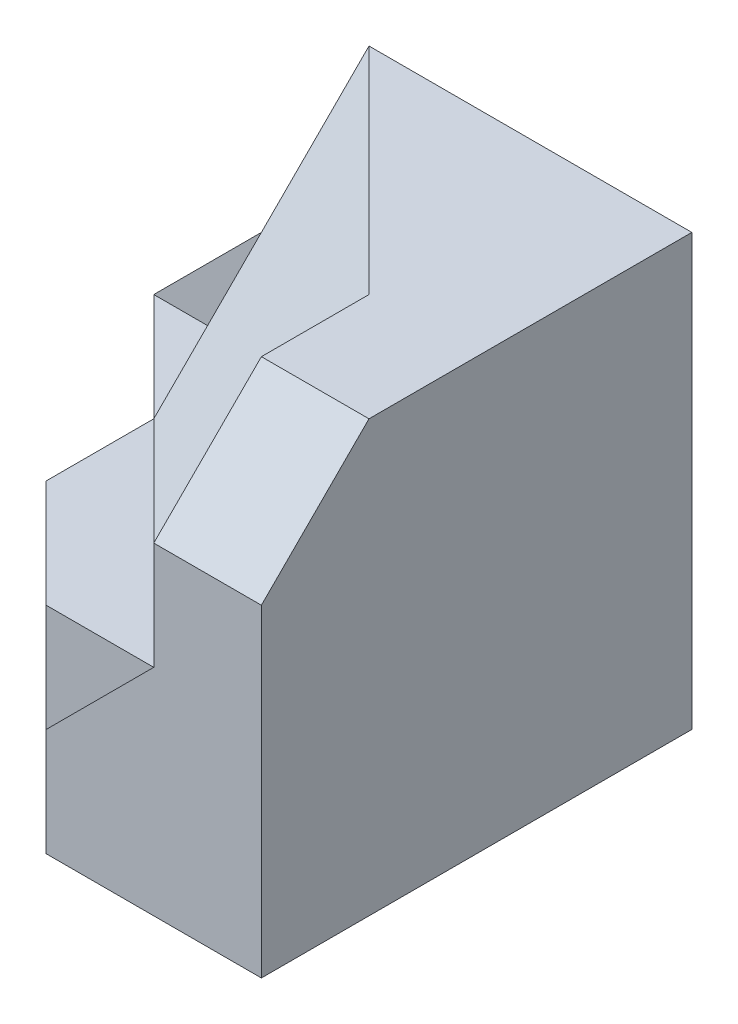
SolidWorks part; units mm, degrees
ref_plane "Front Plane" through (0, 0, 0) normal (0, 0, 1) x (1, 0, 0)
ref_plane "Top Plane" through (0, 0, 0) normal (0, 1, 0) x (1, 0, 0)
ref_plane "Right Plane" through (0, 0, 0) normal (1, 0, 0) x (0, 0, -1)
sketch "Sketch1" plane through (0, 0, 0) normal (0, 1, 0) x (1, 0, 0)
  line L0 (-15, 0) -> (0, 0)
  line L1 (0, 0) -> (0, -15)
  line L2 (0, -15) -> (-5, -15)
  line L3 (-5, -15) -> (-5, -10)
  line L4 (-5, -10) -> (-15, 0)
  dimension "D1" = 5
  dimension "D2" = 5
  dimension "D3" = 15
  dimension "D4" = 15
extrude "Boss-Extrude1" add sketch "Sketch1" against normal blind 20
sketch "Sketch2" plane through (0, 0, 15) normal (0, 0, 1) x (1, 0, 0)
  line L0 (-5, 0) -> (0, 0)
  line L1 (0, 0) -> (0, -20)
  line L2 (0, -20) -> (-5, -20)
  line L3 (-5, -20) -> (-5, 0)
extrude "Boss-Extrude2" add sketch "Sketch2" along normal blind 5
sketch "Sketch3" plane through (-5, 0, 0) normal (-1, 0, 0) x (0, 0, 1)
  line L0 (15, 0) -> (20, -5)
  line L1 (20, 0) -> (20, -20) construction
  line L2 (20, -5) -> (20, 0)
  line L3 (20, 0) -> (15, 0)
  dimension "D1" = 5
  dimension "D2" = 5
extrude "Cut-Extrude1" cut sketch "Sketch3" against normal blind 5
sketch "Sketch4" plane through (-5, 0, 0) normal (-1, 0, 0) x (0, 0, 1)
  line L0 (15, -20) -> (20, -20)
  line L1 (10, -20) -> (20, -20) construction
  line L2 (20, -20) -> (20, -10)
  line L3 (20, -5) -> (20, -20) construction
  line L4 (20, -10) -> (15, -10)
  line L5 (15, -10) -> (15, -20)
  dimension "D1" = 5
  dimension "D2" = 10
extrude "Boss-Extrude3" add sketch "Sketch4" along normal blind 5
sketch "Sketch5" plane through (0, 0, 20) normal (0, 0, 1) x (1, 0, 0)
  line L0 (-5, -10) -> (-10, -15)
  line L1 (-5, -20) -> (-5, 0) construction
  line L2 (-10, -15) -> (-10, -10)
  line L3 (-10, -20) -> (-10, -10) construction
  line L4 (-10, -10) -> (-5, -10) construction
  line L5 (-10, -10) -> (-5, -10)
  dimension "D1" = 5
extrude "Cut-Extrude2" cut sketch "Sketch5" against normal blind 5
ref_plane "Plane1" through (0, -20, 0) normal (0, -1, 0) x (-1, 0, 0)
sketch "Sketch14" plane through (0, -20, 0) normal (0, -1, 0) x (-1, 0, 0)
  line L0 (15, 0) -> (5, -10)
  line L1 (5, -10) -> (5, -15)
  line L2 (5, -15) -> (10, -15)
  line L3 (15, 0) -> (15, -10)
  line L4 (15, -10) -> (10, -15)
  dimension "D1" = 10
extrude "Boss-Extrude31" add sketch "Sketch14" against normal blind 20
sketch3d "3DSketch7"
  line L0 (-5, 0, 15) -> (-5, -10, 15) construction
  line L1 (-10, 0, 15) -> (-10, -15, 15) construction
  line L2 (-15, 0, 10) -> (-15, -20, 10) construction
  line L3 (-5, 0, 15) -> (-10, 0, 15) construction
  line L4 (0, 0, 15) -> (0, 0, 0) construction
  line L5 (-15, 0, 0) -> (-5, 0, 10)
  line L6 (-5, 0, 10) -> (-5, -5, 15)
  line L8 (-5, -5, 15) -> (-10, -10, 15)
  line L9 (-10, -10, 15) -> (-15, -10, 10)
  line L10 (-15, -10, 10) -> (-15, 0, 0)
  point P0 (-15, 0, 0)
  point P1 (-5, 0, 10)
  point P3 (-5, -5, 15)
  point P4 (-10, -10, 15)
  point P7 (-15, -10, 10)
  dimension "D1" = 5
  dimension "D2" = 5
  dimension "D3" = 5
  dimension "D4" = 10
  dimension "D5" = 10
extrude "Cut-Extrude11" cut sketch "3DSketch7" along direction (0, 0, 1) on the side against the normal blind 25
sketch "Sketch24" plane through (-15, 0, 0) normal (-1, 0, 0) x (0, 0, 1)
  line L0 (0, -20) -> (5, -20)
  line L1 (10, -20) -> (0, -20) construction
  line L2 (5, -20) -> (5, -5)
  line L3 (5, -5) -> (0, -5)
  line L4 (0, -20) -> (0, 0) construction
  line L5 (0, -5) -> (0, -20)
  line L6 (0, -5) -> (0, -20)
  line M2 (0, 0) -> (0, -20)
  line M3 (0, -20) -> (10, -20)
  dimension "D1" = 5
  dimension "D2" = 15
extrude "Boss-Extrude32" add sketch "Sketch24" along normal blind 5 contours L2 L3 M2 M3
sketch "Sketch25" plane through (0, 0, 5) normal (0, 0, 1) x (1, 0, 0)
  line L0 (-15, -5) -> (-20, -5)
  line L1 (-20, -5) -> (-20, -10)
  line L2 (-20, -20) -> (-20, -5) construction
  line L3 (-20, -10) -> (-15, -5)
  dimension "D1" = 5
extrude "Cut-Extrude12" cut sketch "Sketch25" against normal blind 5
sketch "Sketch26" plane through (0, -20, 0) normal (0, -1, 0) x (-1, 0, 0)
  line L0 (20, -5) -> (15, -5)
  line L1 (15, -5) -> (15, -10)
  line L2 (15, -10) -> (10, -15)
  line L3 (10, -15) -> (15, -15)
  line L4 (15, -15) -> (20, -10)
  line L5 (20, -10) -> (20, -5)
  dimension "D1" = 5
extrude "Boss-Extrude33" add sketch "Sketch26" against normal blind 5
sketch "Sketch27" plane through (0, -15, 0) normal (0, 1, 0) x (1, 0, 0)
  line L0 (-20, -5) -> (-15, -5)
  line L1 (-15, -5) -> (-15, -10)
  line L2 (-15, -10) -> (-20, -5)
extrude "Boss-Extrude34" add sketch "Sketch27" along normal blind 5
